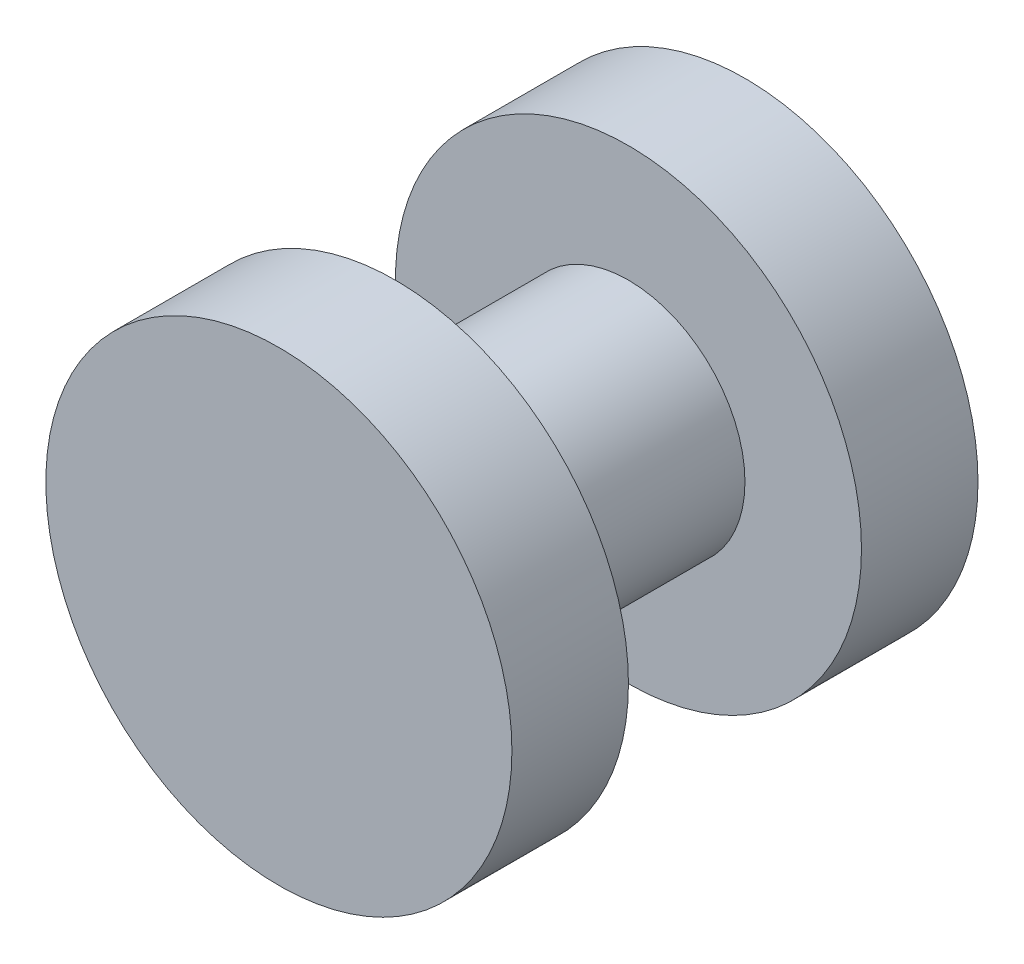
SolidWorks part; units mm, degrees
ref_plane "Front Plane" through (0, 0, 0) normal (0, 0, 1) x (1, 0, 0)
ref_plane "Top Plane" through (0, 0, 0) normal (0, 1, 0) x (1, 0, 0)
ref_plane "Right Plane" through (0, 0, 0) normal (1, 0, 0) x (0, 0, -1)
sketch "Sketch1" plane through (0, 0, 0) normal (0, 0, 1) x (1, 0, 0)
  circle A0 centre (0, 0) radius 6.35
  dimension "D1" = 12.7
extrude "Boss-Extrude2" add sketch "Sketch1" along normal blind 3.175
sketch "Sketch2" plane through (0, 0, 3.175) normal (0, 0, 1) x (1, 0, 0)
  circle A0 centre (0, 0) radius 3.175
  dimension "D1" = 6.35
extrude "Boss-Extrude3" add sketch "Sketch2" along normal blind 6.35
sketch "Sketch3" plane through (0, 0, 9.525) normal (0, 0, 1) x (1, 0, 0)
  circle A0 centre (0, 0) radius 6.35
  dimension "D1" = 12.7
extrude "Boss-Extrude4" add sketch "Sketch3" along normal blind 3.175
